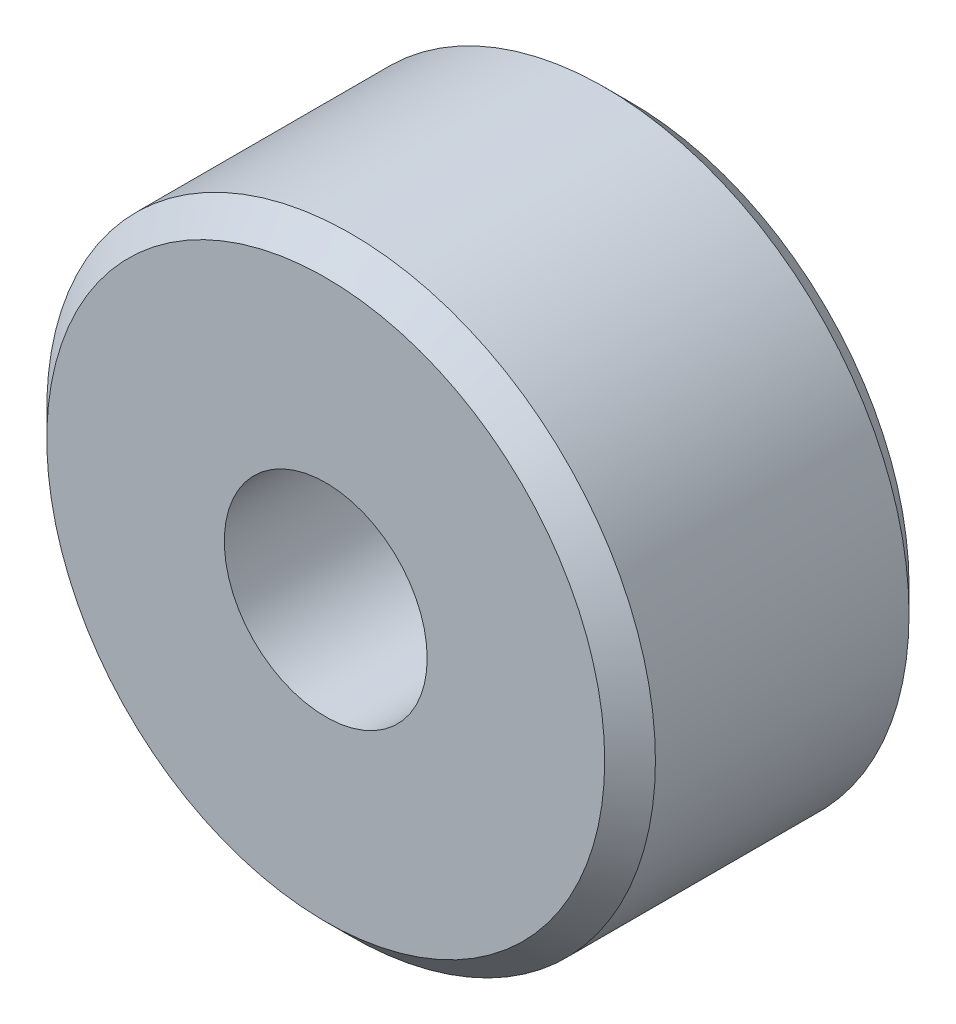
SolidWorks part; units mm, degrees
ref_plane "Ön Düzlem" through (0, 0, 0) normal (0, 0, 1) x (1, 0, 0)
ref_plane "Üst Düzlem" through (0, 0, 0) normal (0, 1, 0) x (1, 0, 0)
ref_plane "Sağ Düzlem" through (0, 0, 0) normal (1, 0, 0) x (0, 0, -1)
sketch "Sketch1" plane through (0, 0, 0) normal (0, 0, 1) x (1, 0, 0)
  circle A0 centre (0, 0) radius 1
  dimension "D1" = 2
extrude "Extrude-Thin1" add sketch "Sketch1" along normal blind 3 thin
chamfer "Chamfer1" distance 0.25 angle 45 2 edges at (3, 0, 0) (3, 0, 3)
